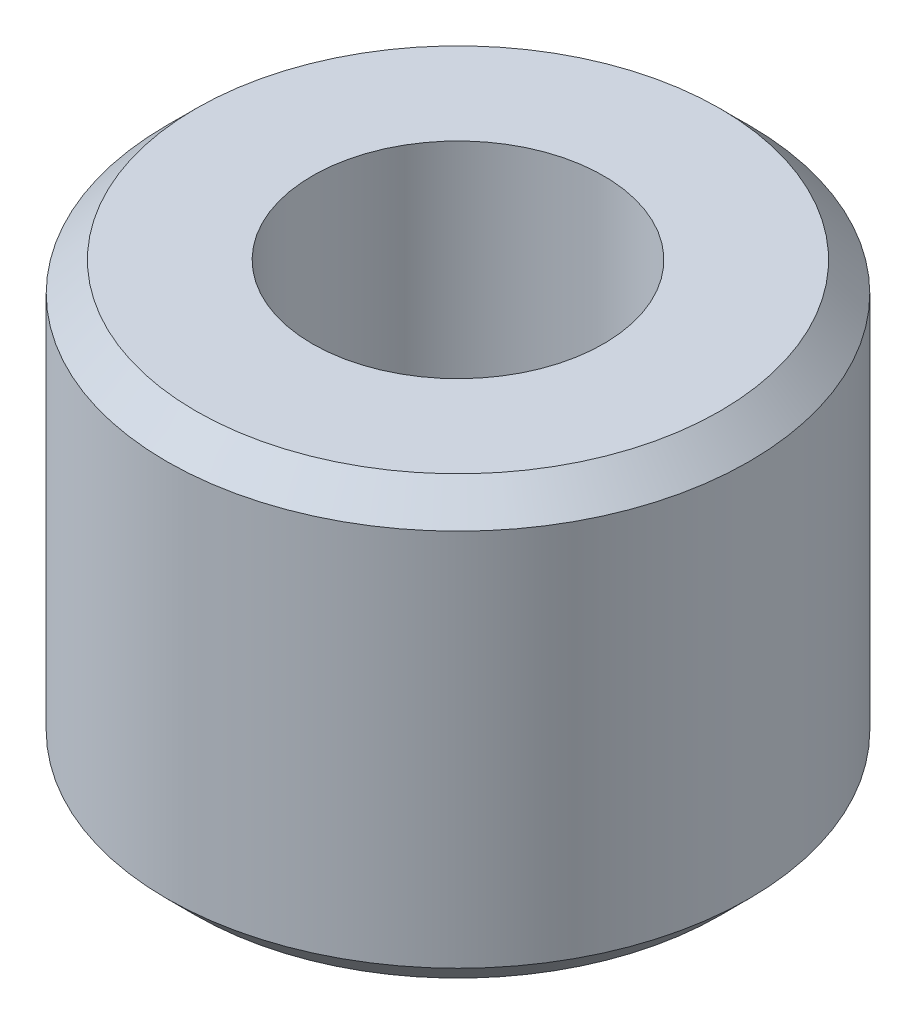
SolidWorks part; units mm, degrees
ref_plane "Front Plane" through (0, 0, 0) normal (0, 0, 1) x (1, 0, 0)
ref_plane "Top Plane" through (0, 0, 0) normal (0, 1, 0) x (1, 0, 0)
ref_plane "Right Plane" through (0, 0, 0) normal (1, 0, 0) x (0, 0, -1)
sketch "Sketch1" plane through (0, 0, 0) normal (0, 1, 0) x (1, 0, 0)
  circle A0 centre (0, 0) radius 10
  circle A1 centre (0, 0) radius 5
extrude "Boss-Extrude1" add sketch "Sketch1" along normal blind 15
chamfer "Chamfer2" distance 1 angle 45 2 edges at (0, 0, 10) (0, 15, 10)
